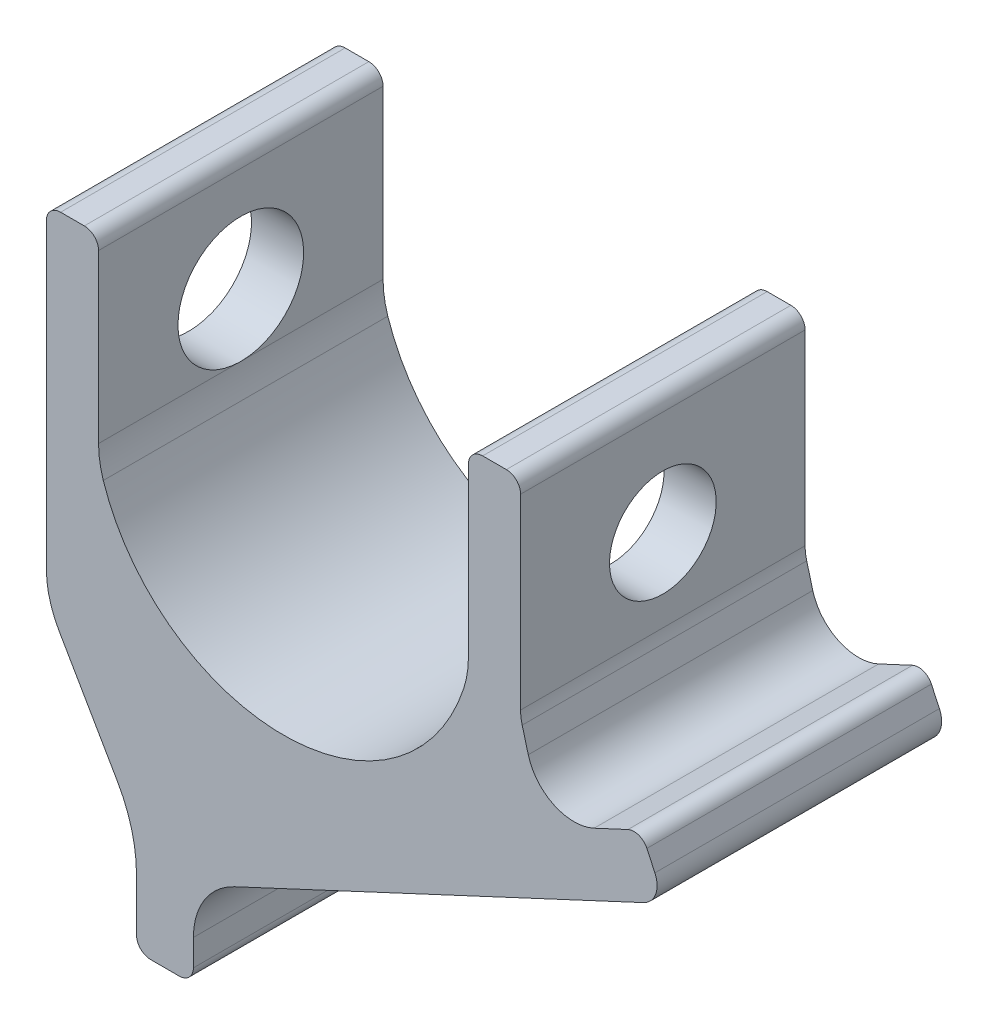
SolidWorks part; units mm, degrees
ref_plane "Front" through (0, 0, 0) normal (0, 0, 1) x (1, 0, 0)
ref_plane "Top" through (0, 0, 0) normal (0, 1, 0) x (1, 0, 0)
ref_plane "Right" through (0, 0, 0) normal (1, 0, 0) x (0, 0, -1)
sketch "Sketch1" plane through (0, 0, 0) normal (0, 0, 1) x (1, 0, 0)
  line L0 (-42.0004, 0) -> (100.6223, 0) construction
  line L1 (-16.264, -7) -> (41.2855, -7) construction
  line L2 (0, -26.4513) -> (0, 47.5409) construction
  line L3 (39, -13.245) -> (39, 22)
  line L4 (42, 25) -> (47, 25)
  line L5 (50, 22) -> (50, -17.4118)
  line L6 (50.3407, -20) -> (51.6186, -24.7692)
  line L7 (65.5041, -31.2441) -> (72.645, -27.9142)
  line L8 (76.6318, -29.3653) -> (78.3223, -32.9905)
  line L9 (75.9038, -39.6352) -> (-10.3393, -79.851)
  line L10 (-35.0192, -72.9474) -> (-47.3205, -51.641)
  line L11 (-50, 22) -> (-50, -41.641)
  line L12 (-42, 25) -> (-47, 25)
  line L13 (-39, -13.245) -> (-39, 22)
  line L14 (-19, -93.4456) -> (-19, -99)
  line L15 (-22, -102) -> (-28, -102)
  line L16 (-31, -99) -> (-31, -87.9474)
  arc A0 (38, -19.49) -> (0, -47) centre (0, -7) cw
  arc A1 (-38, -19.49) -> (0, -47) centre (0, -7) ccw
  arc A2 (47, 25) -> (50, 22) centre (47, 22) cw
  arc A3 (39, 22) -> (42, 25) centre (42, 22) cw
  arc A4 (-42, 25) -> (-39, 22) centre (-42, 22) cw
  arc A5 (-50, 22) -> (-47, 25) centre (-47, 22) cw
  arc A6 (72.645, -27.9142) -> (76.6318, -29.3653) centre (73.9129, -30.6332) cw
  arc A7 (38, -19.49) -> (39, -13.245) centre (19, -13.245) ccw
  arc A8 (-38, -19.49) -> (-39, -13.245) centre (-19, -13.245) cw
  arc A9 (-50, -41.641) -> (-47.3205, -51.641) centre (-30, -41.641) ccw
  arc A10 (51.6186, -24.7692) -> (65.5041, -31.2441) centre (61.2779, -22.181) ccw
  arc A11 (50, -17.4118) -> (50.3407, -20) centre (60, -17.4118) ccw
  arc A12 (-19, -93.4456) -> (-10.3393, -79.851) centre (-4, -93.4456) cw
  arc A13 (-31, -87.9474) -> (-35.0192, -72.9474) centre (-61, -87.9474) ccw
  arc A14 (-28, -102) -> (-31, -99) centre (-28, -99) cw
  arc A15 (-19, -99) -> (-22, -102) centre (-22, -99) cw
  arc A16 (78.3223, -32.9905) -> (75.9038, -39.6352) centre (73.7907, -35.1036) cw
  point P23 (50, 25)
  point P26 (39, 25)
  point P29 (-39, 25)
  point P32 (-50, 25)
  point P37 (39, -15.8882)
  point P40 (-39, -15.8882)
  point P43 (-50, -47)
  point P48 (50, -18.7283)
  dimension "D1" = 40
  dimension "D15" = 3
  dimension "D16" = 20
  dimension "D17" = 10
  dimension "D21" = 15
  dimension "D22" = 30
  dimension "D23" = 3
  dimension "D24" = 5
  dimension "D2" = 25
  dimension "D3" = 78
  dimension "D4" = 11
  dimension "D5" = 15
  dimension "D6" = 12
  dimension "D7" = 25
  dimension "D8" = 7
  dimension "D9" = 30
  dimension "D10" = 72
  dimension "D11" = 20
  dimension "D12" = 68
  dimension "D13" = 60
  dimension "D14" = 90
  dimension "D18" = 12
  dimension "D19" = 127
  dimension "D20" = 19
extrude "Base-Extrude" add sketch "Sketch1" along normal mid plane 60
sketch "Sketch4" plane through (0, 0, 0) normal (0, 0, 1) x (1, 0, 0)
  line L0 (0, 0) -> (66.9004, 0) construction
  line L1 (50, 22) -> (50, -17.4118) construction
  line L2 (50, 11.25) -> (0, 11.25)
  line L3 (0, 11.25) -> (0, 13.25)
  line L4 (0, 13.25) -> (-50, 13.25)
  line L5 (-50, 22) -> (-50, -41.641) construction
  line L6 (-50, 13.25) -> (-50, 0)
  line L7 (-50, 0) -> (0, 0)
  line L8 (50, 11.25) -> (50, 0)
  line L9 (50, 0) -> (0, 0)
  line L10 (42, 25) -> (47, 25) construction
  dimension "D1" = 22.5
  dimension "D2" = 26.5
  dimension "D3" = 25
revolve "Udboring ø26.5/ø22.5" cut sketch "Sketch4" angle 360 about L0
